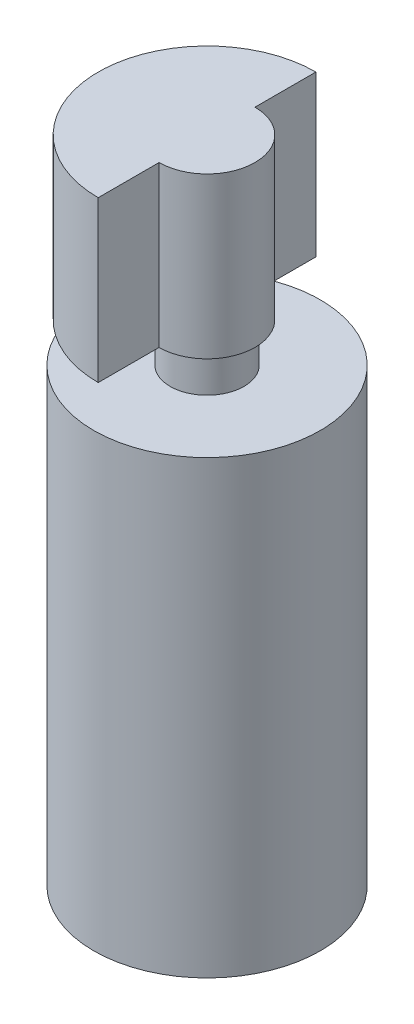
SolidWorks part; units mm, degrees
ref_plane "Front Plane" through (0, 0, 0) normal (0, 0, 1) x (1, 0, 0)
ref_plane "Top Plane" through (0, 0, 0) normal (0, 1, 0) x (1, 0, 0)
ref_plane "Right Plane" through (0, 0, 0) normal (1, 0, 0) x (0, 0, -1)
sketch "Sketch1" plane through (0, 0, 0) normal (0, 1, 0) x (1, 0, 0)
  circle A0 centre (0, 0) radius 3
  dimension "D1" = 6
extrude "Boss-Extrude1" add sketch "Sketch1" along normal blind 11.938
sketch "Sketch2" plane through (0, 11.938, 0) normal (0, 1, 0) x (1, 0, 0)
  circle A0 centre (0, 0) radius 0.9779
  dimension "D1" = 1.9558
extrude "Boss-Extrude2" add sketch "Sketch2" along normal blind 5.2832
sketch "Sketch4" plane through (0, 17.2212, -17.2212) normal (0, -1, 0) x (1, 0, 0)
  line L0 (0, 20.1041) -> (0, 18.4912)
  line L2 (0, 15.9512) -> (0, 14.3383)
  arc A1 (0, 15.9512) -> (0, 18.4912) centre (0, 17.2212) ccw
  arc A2 (0, 20.1041) -> (0, 14.3383) centre (0, 17.2212) ccw
  dimension "D2" = 2.8829
  dimension "D3" = 1.27
extrude "Boss-Extrude3" add sketch "Sketch4" along normal blind 4.2418
